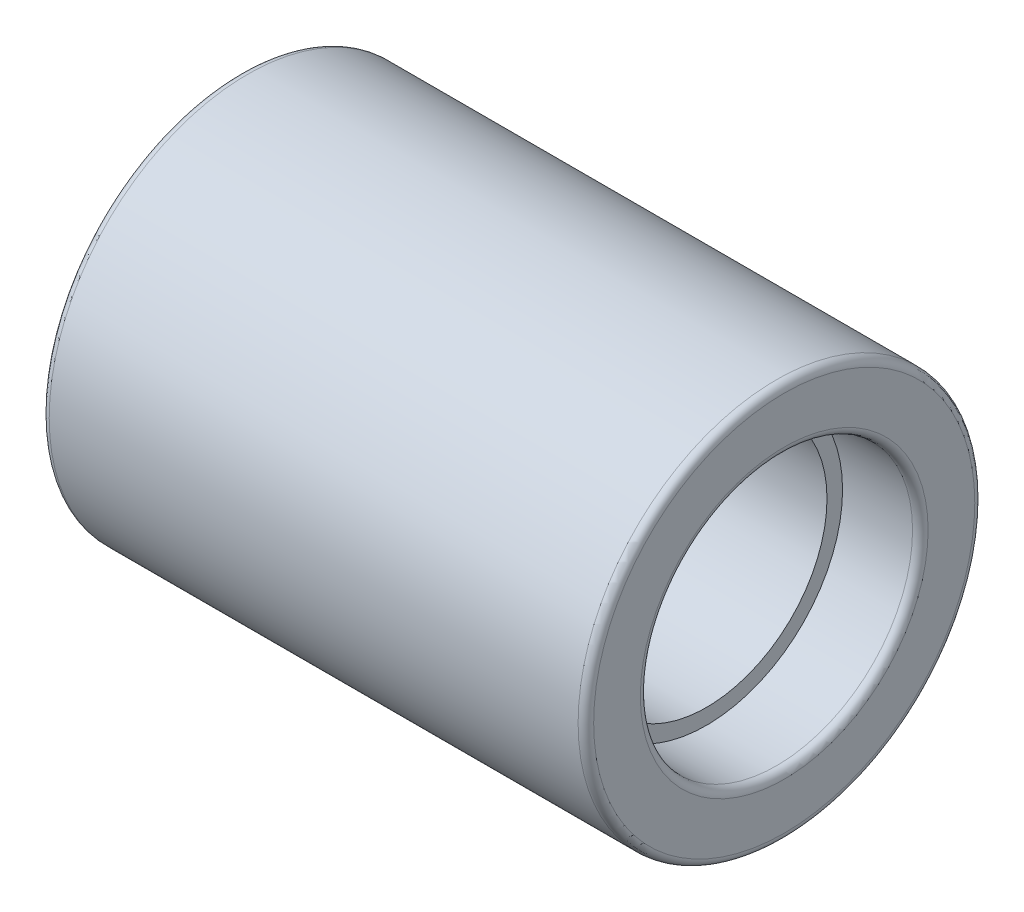
SolidWorks part; units mm, degrees
ref_plane "Front Plane" through (0, 0, 0) normal (0, 0, 1) x (1, 0, 0)
ref_plane "Top Plane" through (0, 0, 0) normal (0, 1, 0) x (1, 0, 0)
ref_plane "Right Plane" through (0, 0, 0) normal (1, 0, 0) x (0, 0, -1)
sketch "Sketch2" plane through (0, 0, 0) normal (1, 0, 0) x (0, 0, -1)
  circle A0 centre (0, 0) radius 25.5
  circle A1 centre (0, 0) radius 15.5
  dimension "D1" = 51
  dimension "D2" = 31
extrude "Boss-Extrude1" add sketch "Sketch2" along normal blind 70
sketch "Sketch3" plane through (70, 0, 0) normal (1, 0, 0) x (0, 0, -1)
  circle A0 centre (0, 0) radius 17.5
  dimension "D1" = 35
extrude "Cut-Extrude1" cut sketch "Sketch3" against normal blind 10
sketch "Sketch4" plane through (0, 0, 0) normal (-1, 0, 0) x (0, 0, 1)
  circle A0 centre (0, 0) radius 17.5
  dimension "D1" = 35
extrude "Cut-Extrude2" cut sketch "Sketch4" against normal blind 10
fillet "Fillet1" radius 1 4 edges at (0, 0, 17.5) (0, 0, -25.5) (70, 0, -17.5) (70, 0, -25.5)
